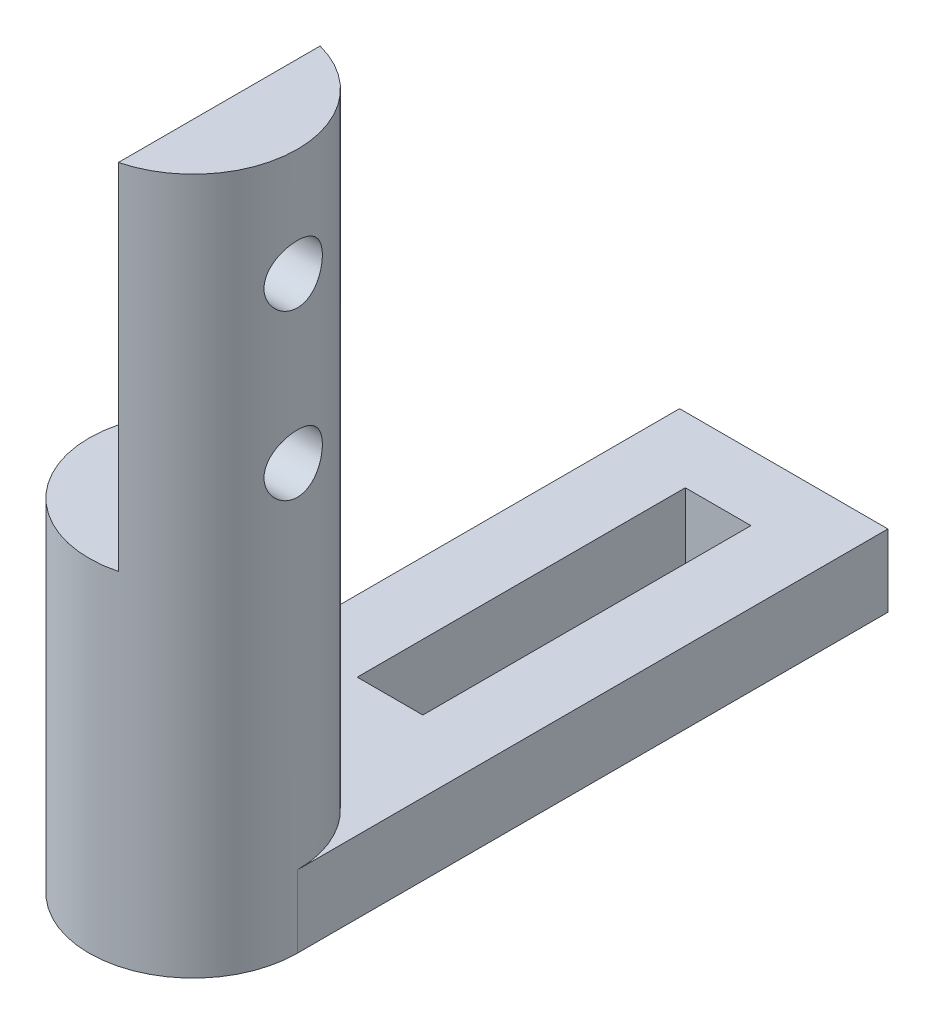
SolidWorks part; units mm, degrees
ref_plane "Front" through (0, 0, 0) normal (0, 0, 1) x (1, 0, 0)
ref_plane "Top" through (0, 0, 0) normal (0, 1, 0) x (1, 0, 0)
ref_plane "Right" through (0, 0, 0) normal (1, 0, 0) x (0, 0, -1)
sketch "草图1" plane through (0, 0, 0) normal (0, 1, 0) x (1, 0, 0)
  circle A0 centre (0, 0) radius 3.175
extrude "凸台-拉伸1" add sketch "草图1" along normal blind 57.15
sketch "草图2" plane through (0, 57.15, 0) normal (0, 1, 0) x (1, 0, 0)
  line L0 (0, 0) -> (0, 3.175) construction
  line L1 (-0.794, 3.175) -> (0.794, 3.175)
  line L2 (0.794, 3.175) -> (0.794, -3.175)
  line L3 (0.794, -3.175) -> (-3.175, -3.175)
  line L4 (-3.175, -3.175) -> (-3.175, 3.175)
  line L5 (-3.175, 3.175) -> (-0.794, 3.175)
  line L6 (0, 0) -> (0.794, 0) construction
  circle A0 centre (0, 0) radius 3.175 construction
  point P8 (0, 3.175)
extrude "切除-拉伸1" cut sketch "草图2" against normal blind 10.795
sketch "草图3" plane through (0.794, 0, 0) normal (-1, 0, 0) x (0, 0, 1)
  line L0 (0, 57.15) -> (0, 53.855) construction
  line L1 (3.0741, 57.15) -> (-3.0741, 57.15) construction
  line L2 (0, 57.15) -> (0, 48.855) construction
  line L3 (0, 53.855) -> (0, 57.15) construction
  circle A0 centre (0, 53.855) radius 0.889
  circle A1 centre (0, 48.855) radius 0.889
extrude "切除-拉伸2" cut sketch "草图3" against normal blind 10.795
sketch "草图4" plane through (0, 0, 0) normal (0, -1, 0) x (1, 0, 0)
  circle A0 centre (0, 0) radius 3.175
extrude "切除-拉伸3" cut sketch "草图4" against normal blind 37.03
sketch "草图5" plane through (0, 37.03, 0) normal (0, -1, 0) x (1, 0, 0)
  line L0 (0, 0) -> (3.175, 0) construction
  line L1 (3.175, 0) -> (3.175, -18) construction
  line L2 (3.175, -18) -> (-3.175, -18) construction
  line L3 (-3.175, -18) -> (-3.175, 0) construction
  line L4 (0, -18) -> (0, -16) construction
  line L6 (3.175, 0) -> (3.175, -18)
  line L7 (3.175, -18) -> (-3.175, -18)
  line L8 (-3.175, -18) -> (-3.175, 0)
  line L9 (0, -9) -> (0, 0) construction
  line L10 (-1, -16) -> (1, -16)
  line L11 (1, -16) -> (1, -6)
  line L12 (1, -6) -> (-1, -6)
  line L13 (-1, -6) -> (-1, -16)
  circle A0 centre (0, 0) radius 3.175 construction
  arc A2 (3.175, 0) -> (-3.175, 0) centre (0, 0) ccw
  point P15 (0, -16)
extrude "凸台-拉伸2" add sketch "草图5" along normal mid plane 2.2
